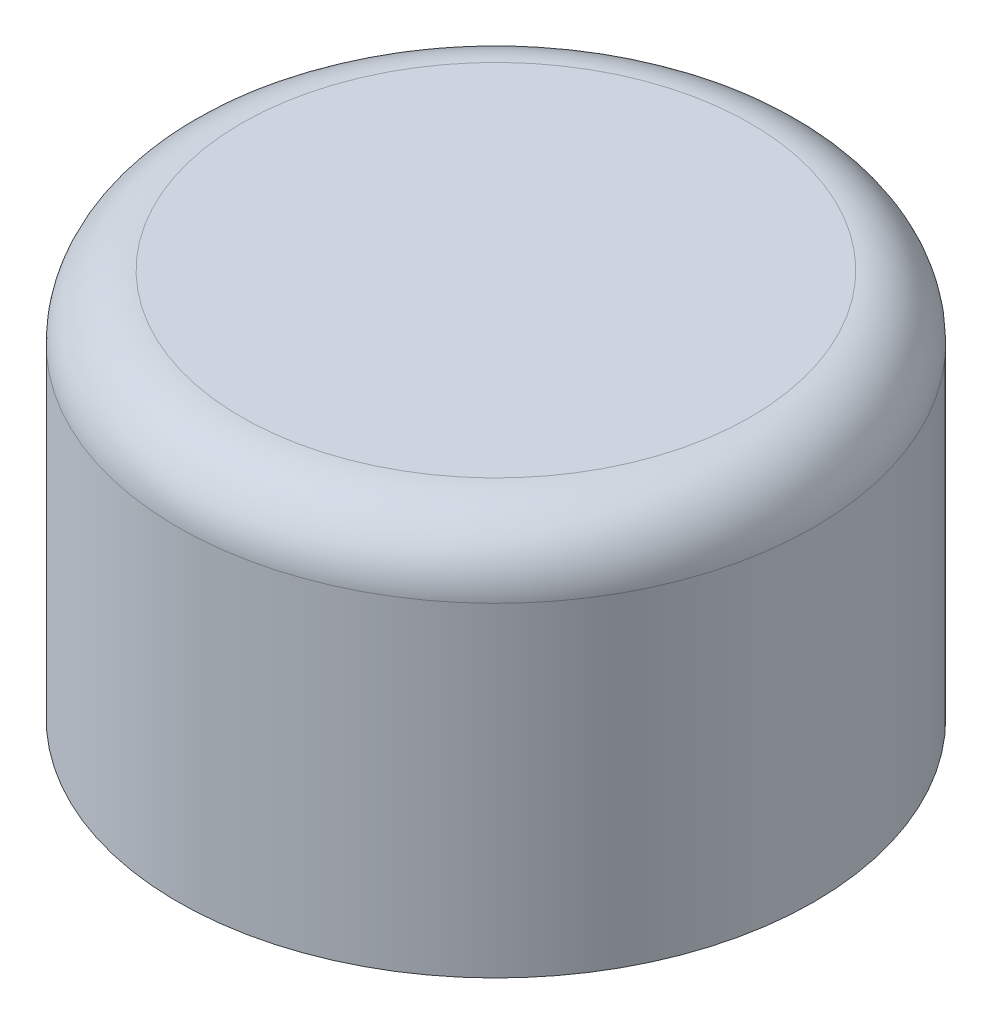
SolidWorks part; units mm, degrees
ref_plane "Front Plane" through (0, 0, 0) normal (0, 0, 1) x (1, 0, 0)
ref_plane "Top Plane" through (0, 0, 0) normal (0, 1, 0) x (1, 0, 0)
ref_plane "Right Plane" through (0, 0, 0) normal (1, 0, 0) x (0, 0, -1)
sketch "Sketch1" plane through (0, 0, 0) normal (0, 0, 1) x (1, 0, 0)
  line L0 (0, 0) -> (0, 12.954) construction
  line L1 (0, 12.954) -> (-10.16, 12.954)
  line L2 (-10.16, 12.954) -> (-10.16, 0)
  line L3 (-10.16, 0) -> (-12.7, 0)
  line L4 (-12.7, 0) -> (-12.7, 12.954)
  line L5 (-10.16, 15.494) -> (0, 15.494)
  line L6 (0, 15.494) -> (0, 12.954)
  arc A0 (-12.7, 12.954) -> (-10.16, 15.494) centre (-10.16, 12.954) cw
  point P4 (-10.16, 7.9692)
  dimension "D4" = 2.54
  dimension "D1" = 2.54
  dimension "D2" = 10.16
  dimension "D3" = 12.954
revolve "Revolve1" add sketch "Sketch1" angle 360 about L0
